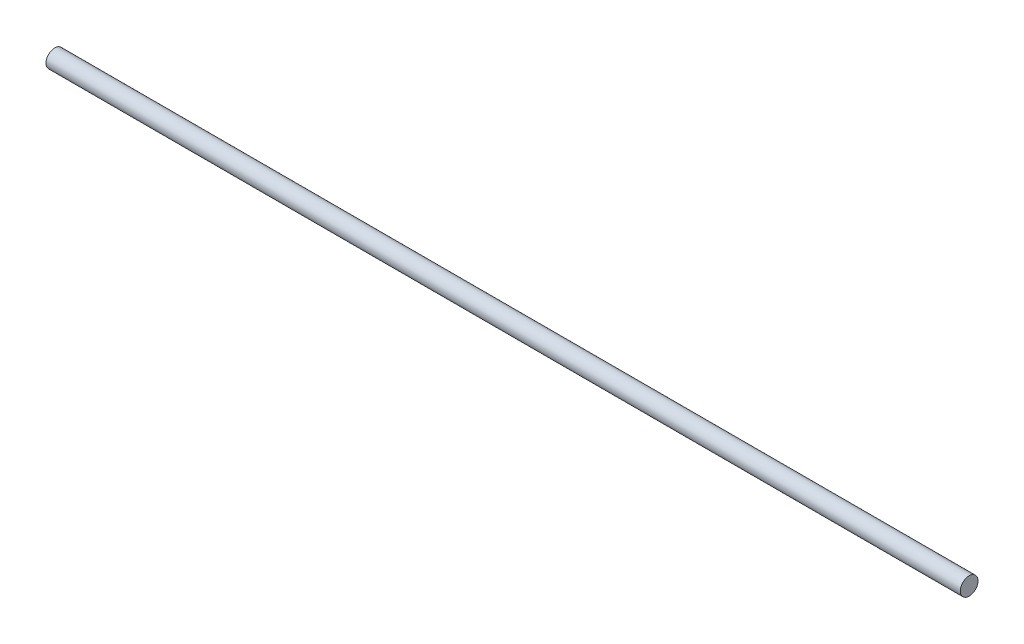
SolidWorks part; units mm, degrees
material "1023 Carbon Steel Sheet (SS)"
ref_plane "Front Plane" through (0, 0, 0) normal (0, 0, 1) x (1, 0, 0)
ref_plane "Top Plane" through (0, 0, 0) normal (0, 1, 0) x (1, 0, 0)
ref_plane "Right Plane" through (0, 0, 0) normal (1, 0, 0) x (0, 0, -1)
sketch "Sketch1" plane through (0, 0, 0) normal (1, 0, 0) x (0, 0, -1)
  circle A0 centre (0, 0) radius 10.795
  dimension "D1" = 21.59
extrude "Boss-Extrude1" add sketch "Sketch1" along normal mid plane 1117.6
